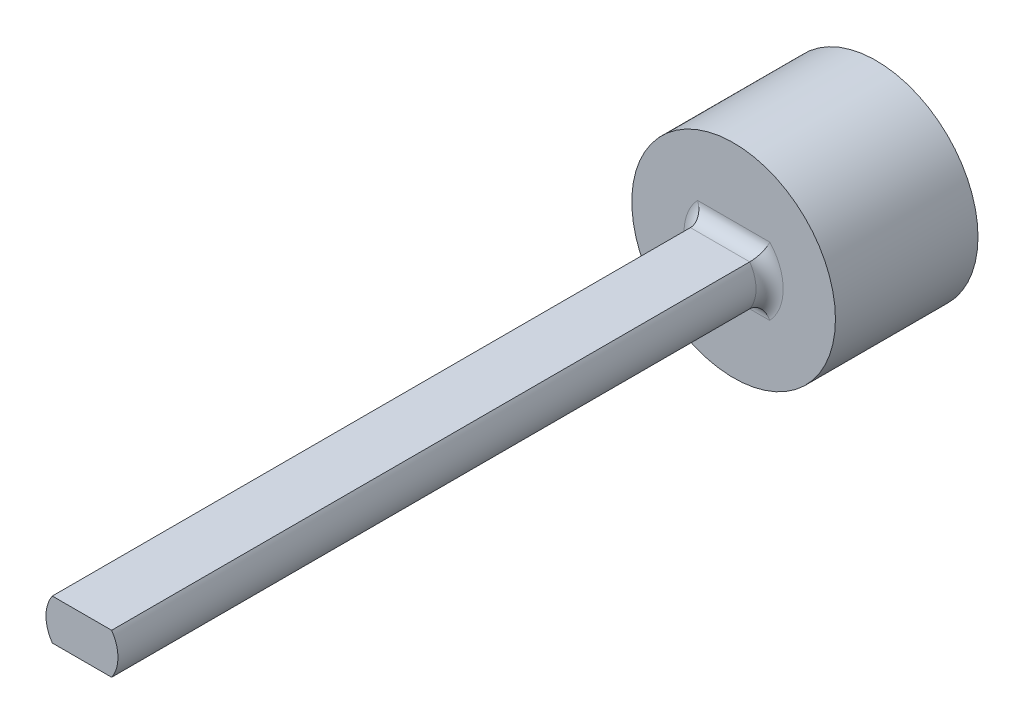
SolidWorks part; units mm, degrees
material "Polylactic Acid (PLA)"
ref_plane "Front Plane" through (0, 0, 0) normal (0, 0, 1) x (1, 0, 0)
ref_plane "Top Plane" through (0, 0, 0) normal (0, 1, 0) x (1, 0, 0)
ref_plane "Right Plane" through (0, 0, 0) normal (1, 0, 0) x (0, 0, -1)
sketch "Sketch2" plane through (0, 0, 0) normal (0, 0, 1) x (1, 0, 0)
  arc A0 (-180.9646, 16.9181) -> (-181.2813, 16.5945) centre (-180.7258, 16.3677) ccw
  arc A1 (-181.2813, 16.5945) -> (-181.4587, 15.6283) centre (-179.0594, 15.6871) ccw
  arc A2 (-181.4587, 15.6283) -> (-180.9368, 15.2683) centre (-178.5779, 19.2465) ccw
  arc A3 (-180.9368, 15.2683) -> (-180.0966, 15.7774) centre (-181.7341, 17.532) ccw
  arc A4 (-180.0966, 15.7774) -> (-179.9066, 16.1884) centre (-180.506, 16.216) ccw
  arc A5 (-179.7695, 16.2766) -> (-179.9066, 16.1884) centre (-179.8067, 16.1838) ccw
  arc A6 (-179.7695, 16.2766) -> (-179.5312, 16.1918) centre (-178.5779, 19.2465) ccw
  arc A7 (-179.4806, 16.0368) -> (-179.5312, 16.1918) centre (-179.561, 16.0963) ccw
  arc A8 (-179.4806, 16.0368) -> (-179.5931, 15.5981) centre (-178.9987, 15.6794) ccw
  arc A9 (-179.5931, 15.5981) -> (-179.2637, 14.6726) centre (-177.2152, 15.9232) ccw
  arc A10 (-179.2637, 14.6726) -> (-178.6317, 14.6218) centre (-178.5779, 19.2465) ccw
  arc A11 (-178.6317, 14.6218) -> (-178.1586, 15.4828) centre (-180.454, 16.1836) ccw
  arc A12 (-178.1586, 15.4828) -> (-178.1996, 15.9338) centre (-178.7324, 15.658) ccw
  arc A13 (-178.1249, 16.0787) -> (-178.1996, 15.9338) centre (-178.1108, 15.9797) ccw
  arc A14 (-178.1249, 16.0787) -> (-177.8761, 16.1244) centre (-178.5779, 19.2465) ccw
  arc A15 (-177.7548, 16.0154) -> (-177.8761, 16.1244) centre (-177.8542, 16.0268) ccw
  arc A16 (-177.7548, 16.0154) -> (-177.6329, 15.5793) centre (-177.1587, 15.9469) ccw
  arc A17 (-177.6329, 15.5793) -> (-176.8848, 14.9425) centre (-175.7362, 17.0498) ccw
  arc A18 (-176.8848, 14.9425) -> (-176.3121, 15.2145) centre (-178.5779, 19.2465) ccw
  arc A19 (-176.3121, 15.2145) -> (-176.3329, 16.1967) centre (-178.6712, 15.6559) ccw
  arc A20 (-176.3329, 16.1967) -> (-176.5939, 16.5668) centre (-176.9175, 16.0615) ccw
  arc A21 (-176.6017, 16.7296) -> (-176.5939, 16.5668) centre (-176.54, 16.651) ccw
  arc A22 (-176.6017, 16.7296) -> (-176.4091, 16.8936) centre (-178.5779, 19.2465) ccw
  arc A23 (-176.2496, 16.8599) -> (-176.4091, 16.8936) centre (-176.3413, 16.8201) ccw
  arc A24 (-176.2496, 16.8599) -> (-175.926, 16.5431) centre (-175.6991, 17.0986) ccw
  arc A25 (-175.926, 16.5431) -> (-174.9597, 16.3657) centre (-175.0185, 18.765) ccw
  arc A26 (-174.9597, 16.3657) -> (-174.5997, 16.8876) centre (-178.5779, 19.2465) ccw
  arc A27 (-174.5997, 16.8876) -> (-175.1088, 17.7278) centre (-176.8634, 16.0903) ccw
  arc A28 (-175.1088, 17.7278) -> (-175.5198, 17.9178) centre (-175.5475, 17.3184) ccw
  arc A29 (-175.608, 18.0549) -> (-175.5198, 17.9178) centre (-175.5152, 18.0177) ccw
  arc A30 (-175.608, 18.0549) -> (-175.5232, 18.2932) centre (-178.5779, 19.2465) ccw
  arc A31 (-175.3682, 18.3438) -> (-175.5232, 18.2932) centre (-175.4277, 18.2635) ccw
  arc A32 (-175.3682, 18.3438) -> (-174.9296, 18.2313) centre (-175.0108, 18.8258) ccw
  arc A33 (-174.9296, 18.2313) -> (-174.004, 18.5608) centre (-175.2546, 20.6092) ccw
  arc A34 (-174.004, 18.5608) -> (-173.9532, 19.1927) centre (-178.5779, 19.2465) ccw
  arc A35 (-173.9532, 19.1927) -> (-174.8142, 19.6658) centre (-175.515, 17.3704) ccw
  arc A36 (-174.8142, 19.6658) -> (-175.2652, 19.6248) centre (-174.9894, 19.092) ccw
  arc A37 (-175.4102, 19.6995) -> (-175.2652, 19.6248) centre (-175.3112, 19.7137) ccw
  arc A38 (-175.4102, 19.6995) -> (-175.4558, 19.9483) centre (-178.5779, 19.2465) ccw
  arc A39 (-175.3469, 20.0696) -> (-175.4558, 19.9483) centre (-175.3583, 19.9702) ccw
  arc A40 (-175.3469, 20.0696) -> (-174.9108, 20.1915) centre (-175.2784, 20.6657) ccw
  arc A41 (-174.9108, 20.1915) -> (-174.274, 20.9396) centre (-176.3812, 22.0882) ccw
  arc A42 (-174.274, 20.9396) -> (-174.5459, 21.5123) centre (-178.5779, 19.2465) ccw
  arc A43 (-174.5459, 21.5123) -> (-175.5282, 21.4915) centre (-174.9873, 19.1532) ccw
  arc A44 (-175.5282, 21.4915) -> (-175.8982, 21.2305) centre (-175.3929, 20.9069) ccw
  arc A45 (-176.0611, 21.2227) -> (-175.8982, 21.2305) centre (-175.9824, 21.2845) ccw
  arc A46 (-176.0611, 21.2227) -> (-176.225, 21.4153) centre (-178.5779, 19.2465) ccw
  arc A47 (-176.1913, 21.5749) -> (-176.225, 21.4153) centre (-176.1515, 21.4831) ccw
  arc A48 (-176.1913, 21.5749) -> (-175.8746, 21.8985) centre (-176.43, 22.1253) ccw
  arc A49 (-175.8746, 21.8985) -> (-175.6971, 22.8647) centre (-178.0964, 22.8059) ccw
  arc A50 (-175.6971, 22.8647) -> (-176.219, 23.2247) centre (-178.5779, 19.2465) ccw
  arc A51 (-176.219, 23.2247) -> (-177.0592, 22.7156) centre (-175.4217, 20.961) ccw
  arc A52 (-177.0592, 22.7156) -> (-177.2492, 22.3046) centre (-176.6499, 22.277) ccw
  arc A53 (-177.3864, 22.2164) -> (-177.2492, 22.3046) centre (-177.3491, 22.3092) ccw
  arc A54 (-177.3864, 22.2164) -> (-177.6247, 22.3012) centre (-178.5779, 19.2465) ccw
  arc A55 (-177.6752, 22.4562) -> (-177.6247, 22.3012) centre (-177.5949, 22.3967) ccw
  arc A56 (-177.6752, 22.4562) -> (-177.5627, 22.8948) centre (-178.1572, 22.8136) ccw
  arc A57 (-177.5627, 22.8948) -> (-177.8922, 23.8204) centre (-179.9406, 22.5698) ccw
  arc A58 (-177.8922, 23.8204) -> (-178.5242, 23.8712) centre (-178.5779, 19.2465) ccw
  arc A59 (-178.5242, 23.8712) -> (-178.9973, 23.0102) centre (-176.7018, 22.3094) ccw
  arc A60 (-178.9973, 23.0102) -> (-178.9563, 22.5592) centre (-178.4234, 22.835) ccw
  arc A61 (-179.0309, 22.4143) -> (-178.9563, 22.5592) centre (-179.0451, 22.5133) ccw
  arc A62 (-179.0309, 22.4143) -> (-179.2797, 22.3686) centre (-178.5779, 19.2465) ccw
  arc A63 (-179.401, 22.4776) -> (-179.2797, 22.3686) centre (-179.3017, 22.4661) ccw
  arc A64 (-179.401, 22.4776) -> (-179.5229, 22.9137) centre (-179.9971, 22.546) ccw
  arc A65 (-179.5229, 22.9137) -> (-180.271, 23.5505) centre (-181.4197, 21.4432) ccw
  arc A66 (-180.271, 23.5505) -> (-180.8437, 23.2785) centre (-178.5779, 19.2465) ccw
  arc A67 (-180.8437, 23.2785) -> (-180.8229, 22.2963) centre (-178.4846, 22.8371) ccw
  arc A68 (-180.8229, 22.2963) -> (-180.562, 21.9262) centre (-180.2383, 22.4315) ccw
  arc A69 (-180.5541, 21.7634) -> (-180.562, 21.9262) centre (-180.6159, 21.842) ccw
  arc A70 (-180.5541, 21.7634) -> (-180.7468, 21.5994) centre (-178.5779, 19.2465) ccw
  arc A71 (-180.9063, 21.6331) -> (-180.7468, 21.5994) centre (-180.8145, 21.6729) ccw
  arc A72 (-180.9063, 21.6331) -> (-181.2299, 21.9499) centre (-181.4567, 21.3944) ccw
  arc A73 (-181.2299, 21.9499) -> (-182.1962, 22.1273) centre (-182.1373, 19.728) ccw
  arc A74 (-182.1962, 22.1273) -> (-182.5561, 21.6054) centre (-178.5779, 19.2465) ccw
  arc A75 (-182.5561, 21.6054) -> (-182.047, 20.7652) centre (-180.2924, 22.4027) ccw
  arc A76 (-182.047, 20.7652) -> (-181.636, 20.5752) centre (-181.6084, 21.1746) ccw
  arc A77 (-181.5478, 20.4381) -> (-181.636, 20.5752) centre (-181.6406, 20.4753) ccw
  arc A78 (-181.5478, 20.4381) -> (-181.6326, 20.1997) centre (-178.5779, 19.2465) ccw
  arc A79 (-181.7877, 20.1492) -> (-181.6326, 20.1997) centre (-181.7281, 20.2295) ccw
  arc A80 (-181.7877, 20.1492) -> (-182.2263, 20.2617) centre (-182.145, 19.6672) ccw
  arc A81 (-182.2263, 20.2617) -> (-183.1518, 19.9322) centre (-181.9012, 17.8838) ccw
  arc A82 (-183.1518, 19.9322) -> (-183.2026, 19.3002) centre (-178.5779, 19.2465) ccw
  arc A83 (-183.2026, 19.3002) -> (-182.3416, 18.8272) centre (-181.6408, 21.1226) ccw
  arc A84 (-182.3416, 18.8272) -> (-181.8906, 18.8681) centre (-182.1664, 19.401) ccw
  arc A85 (-181.7457, 18.7935) -> (-181.8906, 18.8681) centre (-181.8447, 18.7793) ccw
  arc A86 (-181.7457, 18.7935) -> (-181.7, 18.5447) centre (-178.5779, 19.2465) ccw
  arc A87 (-181.809, 18.4234) -> (-181.7, 18.5447) centre (-181.7976, 18.5227) ccw
  arc A88 (-181.809, 18.4234) -> (-182.2451, 18.3015) centre (-181.8775, 17.8273) ccw
  arc A89 (-182.2451, 18.3015) -> (-182.8819, 17.5534) centre (-180.7746, 16.4047) ccw
  arc A90 (-182.8819, 17.5534) -> (-182.6099, 16.9807) centre (-178.5779, 19.2465) ccw
  arc A91 (-182.6099, 16.9807) -> (-181.6277, 17.0015) centre (-182.1685, 19.3398) ccw
  arc A92 (-181.6277, 17.0015) -> (-181.2576, 17.2625) centre (-181.7629, 17.5861) ccw
  arc A93 (-181.0948, 17.2703) -> (-181.2576, 17.2625) centre (-181.1734, 17.2085) ccw
  arc A94 (-181.0948, 17.2703) -> (-180.9308, 17.0777) centre (-178.5779, 19.2465) ccw
  arc A95 (-180.9646, 16.9181) -> (-180.9308, 17.0777) centre (-181.0043, 17.0099) ccw
  arc A96 (-180.9248, 16.8264) -> (-181.1887, 16.5567) centre (-180.7258, 16.3677) ccw
  arc A97 (-181.1887, 16.5567) -> (-181.3594, 15.6773) centre (-179.0594, 15.6871) ccw
  arc A98 (-181.3594, 15.6773) -> (-180.9262, 15.3785) centre (-178.5779, 19.2465) ccw
  arc A99 (-180.9262, 15.3785) -> (-180.1648, 15.8505) centre (-181.7341, 17.532) ccw
  arc A100 (-180.1648, 15.8505) -> (-180.0065, 16.193) centre (-180.506, 16.216) ccw
  arc A101 (-179.7323, 16.3694) -> (-180.0065, 16.193) centre (-179.8067, 16.1838) ccw
  arc A102 (-179.7323, 16.3694) -> (-179.5014, 16.2872) centre (-178.5779, 19.2465) ccw
  arc A103 (-179.4003, 15.9772) -> (-179.5014, 16.2872) centre (-179.561, 16.0963) ccw
  arc A104 (-179.4003, 15.9772) -> (-179.494, 15.6117) centre (-178.9987, 15.6794) ccw
  arc A105 (-179.494, 15.6117) -> (-179.2022, 14.7648) centre (-177.2152, 15.9232) ccw
  arc A106 (-179.2022, 14.7648) -> (-178.6776, 14.7226) centre (-178.5779, 19.2465) ccw
  arc A107 (-178.6776, 14.7226) -> (-178.2542, 15.512) centre (-180.454, 16.1836) ccw
  arc A108 (-178.2542, 15.512) -> (-178.2884, 15.8878) centre (-178.7324, 15.658) ccw
  arc A109 (-178.1391, 16.1777) -> (-178.2884, 15.8878) centre (-178.1108, 15.9797) ccw
  arc A110 (-178.1391, 16.1777) -> (-177.898, 16.222) centre (-178.5779, 19.2465) ccw
  arc A111 (-177.6555, 16.004) -> (-177.898, 16.222) centre (-177.8542, 16.0268) ccw
  arc A112 (-177.6555, 16.004) -> (-177.5539, 15.6406) centre (-177.1587, 15.9469) ccw
  arc A113 (-177.5539, 15.6406) -> (-176.8777, 15.0531) centre (-175.7362, 17.0498) ccw
  arc A114 (-176.8777, 15.0531) -> (-176.4023, 15.2788) centre (-178.5779, 19.2465) ccw
  arc A115 (-176.4023, 15.2788) -> (-176.4304, 16.1742) centre (-178.6712, 15.6559) ccw
  arc A116 (-176.4304, 16.1742) -> (-176.6478, 16.4826) centre (-176.9175, 16.0615) ccw
  arc A117 (-176.6635, 16.8083) -> (-176.6478, 16.4826) centre (-176.54, 16.651) ccw
  arc A118 (-176.6635, 16.8083) -> (-176.4769, 16.9671) centre (-178.5779, 19.2465) ccw
  arc A119 (-176.1578, 16.8996) -> (-176.4769, 16.9671) centre (-176.3413, 16.8201) ccw
  arc A120 (-176.1578, 16.8996) -> (-175.8881, 16.6357) centre (-175.6991, 17.0986) ccw
  arc A121 (-175.8881, 16.6357) -> (-175.0088, 16.465) centre (-175.0185, 18.765) ccw
  arc A122 (-175.0088, 16.465) -> (-174.71, 16.8982) centre (-178.5779, 19.2465) ccw
  arc A123 (-174.71, 16.8982) -> (-175.1819, 17.6596) centre (-176.8634, 16.0903) ccw
  arc A124 (-175.1819, 17.6596) -> (-175.5244, 17.8179) centre (-175.5475, 17.3184) ccw
  arc A125 (-175.7009, 18.0922) -> (-175.5244, 17.8179) centre (-175.5152, 18.0177) ccw
  arc A126 (-175.7009, 18.0922) -> (-175.6187, 18.323) centre (-178.5779, 19.2465) ccw
  arc A127 (-175.3086, 18.4241) -> (-175.6187, 18.323) centre (-175.4277, 18.2635) ccw
  arc A128 (-175.3086, 18.4241) -> (-174.9431, 18.3304) centre (-175.0108, 18.8258) ccw
  arc A129 (-174.9431, 18.3304) -> (-174.0962, 18.6222) centre (-175.2546, 20.6092) ccw
  arc A130 (-174.0962, 18.6222) -> (-174.054, 19.1468) centre (-178.5779, 19.2465) ccw
  arc A131 (-174.054, 19.1468) -> (-174.8434, 19.5702) centre (-175.515, 17.3704) ccw
  arc A132 (-174.8434, 19.5702) -> (-175.2192, 19.536) centre (-174.9894, 19.092) ccw
  arc A133 (-175.5091, 19.6853) -> (-175.2192, 19.536) centre (-175.3112, 19.7137) ccw
  arc A134 (-175.5091, 19.6853) -> (-175.5534, 19.9264) centre (-178.5779, 19.2465) ccw
  arc A135 (-175.3354, 20.1689) -> (-175.5534, 19.9264) centre (-175.3583, 19.9702) ccw
  arc A136 (-175.3354, 20.1689) -> (-174.972, 20.2705) centre (-175.2784, 20.6657) ccw
  arc A137 (-174.972, 20.2705) -> (-174.3845, 20.9467) centre (-176.3812, 22.0882) ccw
  arc A138 (-174.3845, 20.9467) -> (-174.6103, 21.4221) centre (-178.5779, 19.2465) ccw
  arc A139 (-174.6103, 21.4221) -> (-175.5056, 21.3941) centre (-174.9873, 19.1532) ccw
  arc A140 (-175.5056, 21.3941) -> (-175.814, 21.1766) centre (-175.3929, 20.9069) ccw
  arc A141 (-176.1397, 21.1609) -> (-175.814, 21.1766) centre (-175.9824, 21.2845) ccw
  arc A142 (-176.1397, 21.1609) -> (-176.2986, 21.3476) centre (-178.5779, 19.2465) ccw
  arc A143 (-176.2311, 21.6666) -> (-176.2986, 21.3476) centre (-176.1515, 21.4831) ccw
  arc A144 (-176.2311, 21.6666) -> (-175.9671, 21.9363) centre (-176.43, 22.1253) ccw
  arc A145 (-175.9671, 21.9363) -> (-175.7964, 22.8156) centre (-178.0964, 22.8059) ccw
  arc A146 (-175.7964, 22.8156) -> (-176.2296, 23.1145) centre (-178.5779, 19.2465) ccw
  arc A147 (-176.2296, 23.1145) -> (-176.991, 22.6425) centre (-175.4217, 20.961) ccw
  arc A148 (-176.991, 22.6425) -> (-177.1493, 22.3) centre (-176.6499, 22.277) ccw
  arc A149 (-177.4236, 22.1236) -> (-177.1493, 22.3) centre (-177.3491, 22.3092) ccw
  arc A150 (-177.4236, 22.1236) -> (-177.6545, 22.2058) centre (-178.5779, 19.2465) ccw
  arc A151 (-177.7555, 22.5158) -> (-177.6545, 22.2058) centre (-177.5949, 22.3967) ccw
  arc A152 (-177.7555, 22.5158) -> (-177.6618, 22.8813) centre (-178.1572, 22.8136) ccw
  arc A153 (-177.6618, 22.8813) -> (-177.9536, 23.7282) centre (-179.9406, 22.5698) ccw
  arc A154 (-177.9536, 23.7282) -> (-178.4782, 23.7704) centre (-178.5779, 19.2465) ccw
  arc A155 (-178.4782, 23.7704) -> (-178.9016, 22.981) centre (-176.7018, 22.3094) ccw
  arc A156 (-178.9016, 22.981) -> (-178.8675, 22.6052) centre (-178.4234, 22.835) ccw
  arc A157 (-179.0168, 22.3153) -> (-178.8675, 22.6052) centre (-179.0451, 22.5133) ccw
  arc A158 (-179.0168, 22.3153) -> (-179.2578, 22.271) centre (-178.5779, 19.2465) ccw
  arc A159 (-179.5004, 22.489) -> (-179.2578, 22.271) centre (-179.3017, 22.4661) ccw
  arc A160 (-179.5004, 22.489) -> (-179.6019, 22.8524) centre (-179.9971, 22.546) ccw
  arc A161 (-179.6019, 22.8524) -> (-180.2781, 23.4399) centre (-181.4197, 21.4432) ccw
  arc A162 (-180.2781, 23.4399) -> (-180.7535, 23.2142) centre (-178.5779, 19.2465) ccw
  arc A163 (-180.7535, 23.2142) -> (-180.7255, 22.3188) centre (-178.4846, 22.8371) ccw
  arc A164 (-180.7255, 22.3188) -> (-180.508, 22.0104) centre (-180.2383, 22.4315) ccw
  arc A165 (-180.4924, 21.6847) -> (-180.508, 22.0104) centre (-180.6159, 21.842) ccw
  arc A166 (-180.4924, 21.6847) -> (-180.679, 21.5259) centre (-178.5779, 19.2465) ccw
  arc A167 (-180.998, 21.5933) -> (-180.679, 21.5259) centre (-180.8145, 21.6729) ccw
  arc A168 (-180.998, 21.5933) -> (-181.2677, 21.8573) centre (-181.4567, 21.3944) ccw
  arc A169 (-181.2677, 21.8573) -> (-182.1471, 22.028) centre (-182.1373, 19.728) ccw
  arc A170 (-182.1471, 22.028) -> (-182.4459, 21.5948) centre (-178.5779, 19.2465) ccw
  arc A171 (-182.4459, 21.5948) -> (-181.9739, 20.8334) centre (-180.2924, 22.4027) ccw
  arc A172 (-181.9739, 20.8334) -> (-181.6314, 20.6751) centre (-181.6084, 21.1746) ccw
  arc A173 (-181.455, 20.4008) -> (-181.6314, 20.6751) centre (-181.6406, 20.4753) ccw
  arc A174 (-181.455, 20.4008) -> (-181.5372, 20.17) centre (-178.5779, 19.2465) ccw
  arc A175 (-181.8472, 20.0689) -> (-181.5372, 20.17) centre (-181.7281, 20.2295) ccw
  arc A176 (-181.8472, 20.0689) -> (-182.2127, 20.1626) centre (-182.145, 19.6672) ccw
  arc A177 (-182.2127, 20.1626) -> (-183.0597, 19.8708) centre (-181.9012, 17.8838) ccw
  arc A178 (-183.0597, 19.8708) -> (-183.1018, 19.3462) centre (-178.5779, 19.2465) ccw
  arc A179 (-183.1018, 19.3462) -> (-182.3124, 18.9228) centre (-181.6408, 21.1226) ccw
  arc A180 (-182.3124, 18.9228) -> (-181.9366, 18.9569) centre (-182.1664, 19.401) ccw
  arc A181 (-181.6467, 18.8076) -> (-181.9366, 18.9569) centre (-181.8447, 18.7793) ccw
  arc A182 (-181.6467, 18.8076) -> (-181.6024, 18.5666) centre (-178.5779, 19.2465) ccw
  arc A183 (-181.8204, 18.324) -> (-181.6024, 18.5666) centre (-181.7976, 18.5227) ccw
  arc A184 (-181.8204, 18.324) -> (-182.1838, 18.2225) centre (-181.8775, 17.8273) ccw
  arc A185 (-182.1838, 18.2225) -> (-182.7714, 17.5463) centre (-180.7746, 16.4047) ccw
  arc A186 (-182.7714, 17.5463) -> (-182.5456, 17.0709) centre (-178.5779, 19.2465) ccw
  arc A187 (-182.5456, 17.0709) -> (-181.6502, 17.0989) centre (-182.1685, 19.3398) ccw
  arc A188 (-181.6502, 17.0989) -> (-181.3419, 17.3164) centre (-181.7629, 17.5861) ccw
  arc A189 (-181.0161, 17.332) -> (-181.3419, 17.3164) centre (-181.1734, 17.2085) ccw
  arc A190 (-181.0161, 17.332) -> (-180.8573, 17.1454) centre (-178.5779, 19.2465) ccw
  arc A191 (-180.9248, 16.8264) -> (-180.8573, 17.1454) centre (-181.0043, 17.0099) ccw
  arc A192 (-180.9248, 16.8264) -> (-181.1887, 16.5567) centre (-180.7258, 16.3677) ccw construction
  arc A193 (-181.1887, 16.5567) -> (-181.3594, 15.6773) centre (-179.0594, 15.6871) ccw construction
  arc A194 (-181.3594, 15.6773) -> (-180.9262, 15.3785) centre (-178.5779, 19.2465) ccw construction
  arc A195 (-180.9262, 15.3785) -> (-180.1648, 15.8505) centre (-181.7341, 17.532) ccw construction
  arc A196 (-180.1648, 15.8505) -> (-180.0065, 16.193) centre (-180.506, 16.216) ccw construction
  arc A197 (-179.7323, 16.3694) -> (-180.0065, 16.193) centre (-179.8067, 16.1838) ccw construction
  arc A198 (-179.7323, 16.3694) -> (-179.5014, 16.2872) centre (-178.5779, 19.2465) ccw construction
  arc A199 (-179.4003, 15.9772) -> (-179.5014, 16.2872) centre (-179.561, 16.0963) ccw construction
  arc A200 (-179.4003, 15.9772) -> (-179.494, 15.6117) centre (-178.9987, 15.6794) ccw construction
  arc A201 (-179.494, 15.6117) -> (-179.2022, 14.7648) centre (-177.2152, 15.9232) ccw construction
  arc A202 (-179.2022, 14.7648) -> (-178.6776, 14.7226) centre (-178.5779, 19.2465) ccw construction
  arc A203 (-178.6776, 14.7226) -> (-178.2542, 15.512) centre (-180.454, 16.1836) ccw construction
  arc A204 (-178.2542, 15.512) -> (-178.2884, 15.8878) centre (-178.7324, 15.658) ccw construction
  arc A205 (-178.1391, 16.1777) -> (-178.2884, 15.8878) centre (-178.1108, 15.9797) ccw construction
  arc A206 (-178.1391, 16.1777) -> (-177.898, 16.222) centre (-178.5779, 19.2465) ccw construction
  arc A207 (-177.6555, 16.004) -> (-177.898, 16.222) centre (-177.8542, 16.0268) ccw construction
  arc A208 (-177.6555, 16.004) -> (-177.5539, 15.6406) centre (-177.1587, 15.9469) ccw construction
  arc A209 (-177.5539, 15.6406) -> (-176.8777, 15.0531) centre (-175.7362, 17.0498) ccw construction
  arc A210 (-176.8777, 15.0531) -> (-176.4023, 15.2788) centre (-178.5779, 19.2465) ccw construction
  arc A211 (-176.4023, 15.2788) -> (-176.4304, 16.1742) centre (-178.6712, 15.6559) ccw construction
  arc A212 (-176.4304, 16.1742) -> (-176.6478, 16.4826) centre (-176.9175, 16.0615) ccw construction
  arc A213 (-176.6635, 16.8083) -> (-176.6478, 16.4826) centre (-176.54, 16.651) ccw construction
  arc A214 (-176.6635, 16.8083) -> (-176.4769, 16.9671) centre (-178.5779, 19.2465) ccw construction
  arc A215 (-176.1578, 16.8996) -> (-176.4769, 16.9671) centre (-176.3413, 16.8201) ccw construction
  arc A216 (-176.1578, 16.8996) -> (-175.8881, 16.6357) centre (-175.6991, 17.0986) ccw construction
  arc A217 (-175.8881, 16.6357) -> (-175.0088, 16.465) centre (-175.0185, 18.765) ccw construction
  arc A218 (-175.0088, 16.465) -> (-174.71, 16.8982) centre (-178.5779, 19.2465) ccw construction
  arc A219 (-174.71, 16.8982) -> (-175.1819, 17.6596) centre (-176.8634, 16.0903) ccw construction
  arc A220 (-175.1819, 17.6596) -> (-175.5244, 17.8179) centre (-175.5475, 17.3184) ccw construction
  arc A221 (-175.7009, 18.0922) -> (-175.5244, 17.8179) centre (-175.5152, 18.0177) ccw construction
  arc A222 (-175.7009, 18.0922) -> (-175.6187, 18.323) centre (-178.5779, 19.2465) ccw construction
  arc A223 (-175.3086, 18.4241) -> (-175.6187, 18.323) centre (-175.4277, 18.2635) ccw construction
  arc A224 (-175.3086, 18.4241) -> (-174.9431, 18.3304) centre (-175.0108, 18.8258) ccw construction
  arc A225 (-174.9431, 18.3304) -> (-174.0962, 18.6222) centre (-175.2546, 20.6092) ccw construction
  arc A226 (-174.0962, 18.6222) -> (-174.054, 19.1468) centre (-178.5779, 19.2465) ccw construction
  arc A227 (-174.054, 19.1468) -> (-174.8434, 19.5702) centre (-175.515, 17.3704) ccw construction
  arc A228 (-174.8434, 19.5702) -> (-175.2192, 19.536) centre (-174.9894, 19.092) ccw construction
  arc A229 (-175.5091, 19.6853) -> (-175.2192, 19.536) centre (-175.3112, 19.7137) ccw construction
  arc A230 (-175.5091, 19.6853) -> (-175.5534, 19.9264) centre (-178.5779, 19.2465) ccw construction
  arc A231 (-175.3354, 20.1689) -> (-175.5534, 19.9264) centre (-175.3583, 19.9702) ccw construction
  arc A232 (-175.3354, 20.1689) -> (-174.972, 20.2705) centre (-175.2784, 20.6657) ccw construction
  arc A233 (-174.972, 20.2705) -> (-174.3845, 20.9467) centre (-176.3812, 22.0882) ccw construction
  arc A234 (-174.3845, 20.9467) -> (-174.6103, 21.4221) centre (-178.5779, 19.2465) ccw construction
  arc A235 (-174.6103, 21.4221) -> (-175.5056, 21.3941) centre (-174.9873, 19.1532) ccw construction
  arc A236 (-175.5056, 21.3941) -> (-175.814, 21.1766) centre (-175.3929, 20.9069) ccw construction
  arc A237 (-176.1397, 21.1609) -> (-175.814, 21.1766) centre (-175.9824, 21.2845) ccw construction
  arc A238 (-176.1397, 21.1609) -> (-176.2986, 21.3476) centre (-178.5779, 19.2465) ccw construction
  arc A239 (-176.2311, 21.6666) -> (-176.2986, 21.3476) centre (-176.1515, 21.4831) ccw construction
  arc A240 (-176.2311, 21.6666) -> (-175.9671, 21.9363) centre (-176.43, 22.1253) ccw construction
  arc A241 (-175.9671, 21.9363) -> (-175.7964, 22.8156) centre (-178.0964, 22.8059) ccw construction
  arc A242 (-175.7964, 22.8156) -> (-176.2296, 23.1145) centre (-178.5779, 19.2465) ccw construction
  arc A243 (-176.2296, 23.1145) -> (-176.991, 22.6425) centre (-175.4217, 20.961) ccw construction
  arc A244 (-176.991, 22.6425) -> (-177.1493, 22.3) centre (-176.6499, 22.277) ccw construction
  arc A245 (-177.4236, 22.1236) -> (-177.1493, 22.3) centre (-177.3491, 22.3092) ccw construction
  arc A246 (-177.4236, 22.1236) -> (-177.6545, 22.2058) centre (-178.5779, 19.2465) ccw construction
  arc A247 (-177.7555, 22.5158) -> (-177.6545, 22.2058) centre (-177.5949, 22.3967) ccw construction
  arc A248 (-177.7555, 22.5158) -> (-177.6618, 22.8813) centre (-178.1572, 22.8136) ccw construction
  arc A249 (-177.6618, 22.8813) -> (-177.9536, 23.7282) centre (-179.9406, 22.5698) ccw construction
  arc A250 (-177.9536, 23.7282) -> (-178.4782, 23.7704) centre (-178.5779, 19.2465) ccw construction
  arc A251 (-178.4782, 23.7704) -> (-178.9016, 22.981) centre (-176.7018, 22.3094) ccw construction
  arc A252 (-178.9016, 22.981) -> (-178.8675, 22.6052) centre (-178.4234, 22.835) ccw construction
  arc A253 (-179.0168, 22.3153) -> (-178.8675, 22.6052) centre (-179.0451, 22.5133) ccw construction
  arc A254 (-179.0168, 22.3153) -> (-179.2578, 22.271) centre (-178.5779, 19.2465) ccw construction
  arc A255 (-179.5004, 22.489) -> (-179.2578, 22.271) centre (-179.3017, 22.4661) ccw construction
  arc A256 (-179.5004, 22.489) -> (-179.6019, 22.8524) centre (-179.9971, 22.546) ccw construction
  arc A257 (-179.6019, 22.8524) -> (-180.2781, 23.4399) centre (-181.4197, 21.4432) ccw construction
  arc A258 (-180.2781, 23.4399) -> (-180.7535, 23.2142) centre (-178.5779, 19.2465) ccw construction
  arc A259 (-180.7535, 23.2142) -> (-180.7255, 22.3188) centre (-178.4846, 22.8371) ccw construction
  arc A260 (-180.7255, 22.3188) -> (-180.508, 22.0104) centre (-180.2383, 22.4315) ccw construction
  arc A261 (-180.4924, 21.6847) -> (-180.508, 22.0104) centre (-180.6159, 21.842) ccw construction
  arc A262 (-180.4924, 21.6847) -> (-180.679, 21.5259) centre (-178.5779, 19.2465) ccw construction
  arc A263 (-180.998, 21.5933) -> (-180.679, 21.5259) centre (-180.8145, 21.6729) ccw construction
  arc A264 (-180.998, 21.5933) -> (-181.2677, 21.8573) centre (-181.4567, 21.3944) ccw construction
  arc A265 (-181.2677, 21.8573) -> (-182.1471, 22.028) centre (-182.1373, 19.728) ccw construction
  arc A266 (-182.1471, 22.028) -> (-182.4459, 21.5948) centre (-178.5779, 19.2465) ccw construction
  arc A267 (-182.4459, 21.5948) -> (-181.9739, 20.8334) centre (-180.2924, 22.4027) ccw construction
  arc A268 (-181.9739, 20.8334) -> (-181.6314, 20.6751) centre (-181.6084, 21.1746) ccw construction
  arc A269 (-181.455, 20.4008) -> (-181.6314, 20.6751) centre (-181.6406, 20.4753) ccw construction
  arc A270 (-181.455, 20.4008) -> (-181.5372, 20.17) centre (-178.5779, 19.2465) ccw construction
  arc A271 (-181.8472, 20.0689) -> (-181.5372, 20.17) centre (-181.7281, 20.2295) ccw construction
  arc A272 (-181.8472, 20.0689) -> (-182.2127, 20.1626) centre (-182.145, 19.6672) ccw construction
  arc A273 (-182.2127, 20.1626) -> (-183.0597, 19.8708) centre (-181.9012, 17.8838) ccw construction
  arc A274 (-183.0597, 19.8708) -> (-183.1018, 19.3462) centre (-178.5779, 19.2465) ccw construction
  arc A275 (-183.1018, 19.3462) -> (-182.3124, 18.9228) centre (-181.6408, 21.1226) ccw construction
  arc A276 (-182.3124, 18.9228) -> (-181.9366, 18.9569) centre (-182.1664, 19.401) ccw construction
  arc A277 (-181.6467, 18.8076) -> (-181.9366, 18.9569) centre (-181.8447, 18.7793) ccw construction
  arc A278 (-181.6467, 18.8076) -> (-181.6024, 18.5666) centre (-178.5779, 19.2465) ccw construction
  arc A279 (-181.8204, 18.324) -> (-181.6024, 18.5666) centre (-181.7976, 18.5227) ccw construction
  arc A280 (-181.8204, 18.324) -> (-182.1838, 18.2225) centre (-181.8775, 17.8273) ccw construction
  arc A281 (-182.1838, 18.2225) -> (-182.7714, 17.5463) centre (-180.7746, 16.4047) ccw construction
  arc A282 (-182.7714, 17.5463) -> (-182.5456, 17.0709) centre (-178.5779, 19.2465) ccw construction
  arc A283 (-182.5456, 17.0709) -> (-181.6502, 17.0989) centre (-182.1685, 19.3398) ccw construction
  arc A284 (-181.6502, 17.0989) -> (-181.3419, 17.3164) centre (-181.7629, 17.5861) ccw construction
  arc A285 (-181.0161, 17.332) -> (-181.3419, 17.3164) centre (-181.1734, 17.2085) ccw construction
  arc A286 (-181.0161, 17.332) -> (-180.8573, 17.1454) centre (-178.5779, 19.2465) ccw construction
  arc A287 (-180.9248, 16.8264) -> (-180.8573, 17.1454) centre (-181.0043, 17.0099) ccw construction
  circle A288 centre (-178.5779, 19.2465) radius 7.5
  dimension "D3" = 15
  dimension "D1" = 0
  dimension "D2" = 0.1
extrude "Boss-Extrude1" add sketch "Sketch2" against normal offset from surface 0.5 and the other way offset from surface (4 mm away) 1
sketch "Sketch4" plane through (0, 0, 4) normal (0, 0, 1) x (1, 0, 0)
  circle A1 centre (-178.5779, 19.2465) radius 7.5
  circle A2 centre (-178.5779, 19.2465) radius 7.5
  dimension "D1" = 0
extrude "Boss-Extrude2" add sketch "Sketch4" along normal blind 1
sketch "Sketch6" plane through (0, 0, 5) normal (0, 0, 1) x (1, 0, 0)
  line L1 (-180.7625, 20.7465) -> (-176.3933, 20.7465)
  line L2 (-180.7625, 20.7465) -> (-180.7625, 17.7465) construction
  line L3 (-180.7625, 17.7465) -> (-176.3933, 17.7465)
  line L4 (-176.3933, 20.7465) -> (-176.3933, 17.7465) construction
  line L5 (-180.7625, 20.7465) -> (-176.3933, 17.7465) construction
  line L6 (-180.7625, 17.7465) -> (-176.3933, 20.7465) construction
  arc A0 (-180.7625, 20.7465) -> (-180.7625, 17.7465) centre (-178.5779, 19.2465) ccw
  arc A1 (-176.3933, 17.7465) -> (-176.3933, 20.7465) centre (-178.5779, 19.2465) ccw
  dimension "D1" = 5.3
  dimension "D2" = 1.5
extrude "Boss-Extrude3" add sketch "Sketch6" along normal blind 48
fillet "Fillet1" radius 1 4 edges at (-181.2279, 19.2465, 5) (-178.5779, 17.7465, 5) (-175.9279, 19.2465, 5) (-178.5779, 20.7465, 5)
ref_plane "Plane1" through (0, 19.2465, 0) normal (0, 1, 0) x (1, 0, 0)
sketch "Sketch7" plane through (0, 19.2465, 0) normal (0, 1, 0) x (1, 0, 0)
  line L1 (-182.2279, -6) -> (-182.2279, -11)
  line L2 (-182.0023, -48) -> (-193.5242, -5)
  line L3 (-187.0779, -6) -> (-185.0779, -6)
  line L5 (-171.0779, 5.5) -> (-186.0779, 5.5) construction
  line L6 (-187.0779, 5.5) -> (-193.5242, 5.5)
  line L7 (-187.0779, 5.5) -> (-187.0779, 5.1)
  line L9 (-193.5242, 5.5) -> (-193.5242, -5)
  line L10 (-186.0779, 5.5) -> (-186.0779, -5) construction
  line L11 (-186.0779, -5) -> (-171.0779, -5) construction
  line L12 (-181.2279, -6) -> (-181.2279, -53) construction
  line L13 (-187.0779, -4.6) -> (-187.0779, -6)
  line L14 (-187.0779, 5.1) -> (-186.0779, 5.1)
  line L16 (-187.0779, -4.6) -> (-186.0779, -4.6)
  line L17 (-186.0779, 5.1) -> (-186.0779, -4.6)
  line L19 (-185.0779, -5) -> (-183.2279, -5)
  line L20 (-185.0779, -5) -> (-185.0779, -6)
  line L22 (-183.2279, -5) -> (-183.2279, -6)
  line L23 (-182.2279, -11) -> (-181.2279, -11)
  line L25 (-182.2279, -17) -> (-181.2279, -17)
  line L26 (-181.2279, -11) -> (-181.2279, -17)
  line L27 (-182.2279, -27) -> (-181.2279, -27)
  line L29 (-182.2279, -30) -> (-181.2279, -30)
  line L30 (-181.2279, -27) -> (-181.2279, -30)
  line L31 (-182.2279, -40) -> (-181.2279, -40)
  line L33 (-182.0023, -48) -> (-181.2279, -48)
  line L34 (-181.2279, -40) -> (-181.2279, -48)
  line L39 (-183.2279, -6) -> (-182.2279, -6)
  line L40 (-182.2279, -17) -> (-182.2279, -27)
  line L41 (-182.2279, -30) -> (-182.2279, -40)
  line L43 (-180.7625, -6) -> (-181.2279, -6) construction
  line L44 (-182.2279, -5) -> (-181.2373, -5) construction
  line L45 (-176.3933, -53) -> (-180.7625, -53) construction
  line L46 (-178.5779, 5.5) -> (-178.5779, -53) construction
  line L47 (-175.1535, -48) -> (-175.9279, -48)
  line L48 (-175.9279, -40) -> (-175.9279, -48)
  line L49 (-174.9279, -40) -> (-175.9279, -40)
  line L50 (-174.9279, -30) -> (-174.9279, -40)
  line L51 (-174.9279, -30) -> (-175.9279, -30)
  line L52 (-175.9279, -27) -> (-175.9279, -30)
  line L53 (-174.9279, -27) -> (-175.9279, -27)
  line L54 (-174.9279, -17) -> (-174.9279, -27)
  line L55 (-174.9279, -17) -> (-175.9279, -17)
  line L56 (-175.9279, -11) -> (-175.9279, -17)
  line L57 (-174.9279, -11) -> (-175.9279, -11)
  line L58 (-174.9279, -6) -> (-174.9279, -11)
  line L59 (-173.9279, -6) -> (-174.9279, -6)
  line L60 (-173.9279, -5) -> (-173.9279, -6)
  line L61 (-172.0779, -5) -> (-173.9279, -5)
  line L62 (-172.0779, -5) -> (-172.0779, -6)
  line L63 (-170.0779, -6) -> (-172.0779, -6)
  line L64 (-170.0779, -4.6) -> (-170.0779, -6)
  line L65 (-170.0779, -4.6) -> (-171.0779, -4.6)
  line L66 (-171.0779, 5.1) -> (-171.0779, -4.6)
  line L67 (-170.0779, 5.1) -> (-171.0779, 5.1)
  line L68 (-170.0779, 5.5) -> (-170.0779, 5.1)
  line L69 (-170.0779, 5.5) -> (-163.6317, 5.5)
  line L70 (-163.6317, 5.5) -> (-163.6317, -5)
  line L71 (-175.1535, -48) -> (-163.6317, -5)
  dimension "D1" = 1
  dimension "D2" = 1
  dimension "D3" = 1
  dimension "D4" = 0.4
  dimension "D5" = 0.4
  dimension "D6" = 1
  dimension "D7" = 1
  dimension "D8" = 5
  dimension "D9" = 10
  dimension "D10" = 10
  dimension "D11" = 5
  dimension "D12" = 12
  dimension "D13" = 25
  dimension "D14" = 15
  dimension "D15" = 15
extrude "Boss-Extrude6" [suppressed] add sketch "Sketch7" along normal mid plane 0.4 separate body
